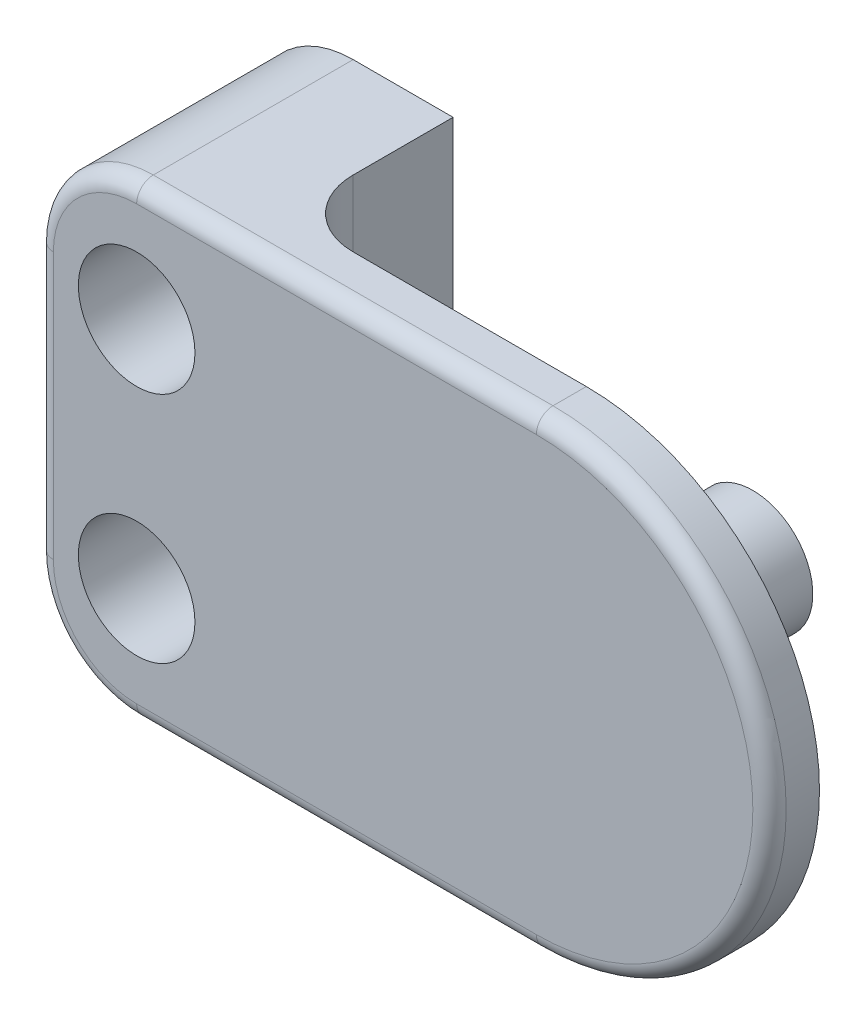
SolidWorks part; units mm, degrees
ref_plane "Front Plane" through (0, 0, 0) normal (0, 0, 1) x (1, 0, 0)
ref_plane "Top Plane" through (0, 0, 0) normal (0, 1, 0) x (1, 0, 0)
ref_plane "Right Plane" through (0, 0, 0) normal (1, 0, 0) x (0, 0, -1)
sketch "Sketch1" plane through (0, 0, 0) normal (0, 0, 1) x (1, 0, 0)
  line L0 (-1.7511, 0) -> (-50001.7511, 0) construction
  line L2 (-15, 7) -> (0, 7)
  line L3 (-15, 7) -> (-15, -7)
  line L4 (-15, -7) -> (0, -7)
  arc A1 (0, 7) -> (0, -7) centre (0, 0) cw
  circle A2 centre (-12, 3.5) radius 1.1
  circle A3 centre (-12, -3.5) radius 1.1
  dimension "D1" = 2.2
  dimension "D2" = 12
  dimension "D3" = 3
  dimension "D4" = 7
  dimension "D5" = 7
extrude "Boss-Extrude1" add sketch "Sketch1" along normal blind 1.5
sketch "Sketch2" plane through (0, 0, 0) normal (0, 0, -1) x (-1, 0, 0)
  circle A0 centre (0, 0) radius 2.5
  dimension "D1" = 5
extrude "Boss-Extrude2" add sketch "Sketch2" along normal blind 1
sketch "Sketch3" plane through (0, 0, -1) normal (0, 0, -1) x (-1, 0, 0)
  line L0 (1.1386, 1.3941) -> (1.1386, -1.3941)
  arc A1 (1.1386, 1.3941) -> (1.1386, -1.3941) centre (0, 0) ccw
  dimension "D1" = 1.8
  dimension "D2" = 1.1386
extrude "Boss-Extrude3" add sketch "Sketch3" along normal blind 4
sketch "Sketch4" plane through (0, 0, 0) normal (0, 0, -1) x (-1, 0, 0)
  line L0 (15, -7) -> (0, -7) construction
  line L1 (15, 7) -> (9, 7)
  line L2 (15, 7) -> (15, -7)
  line L3 (15, -7) -> (9, -7)
  line L4 (9, 7) -> (9, -7)
  circle A0 centre (12, 3.5) radius 1.1
  circle A1 centre (12, -3.5) radius 1.1
  dimension "D1" = 6
extrude "Boss-Extrude4" add sketch "Sketch4" along normal blind 5
fillet "Fillet4" radius 3 2 edges at (-15, 7, -1.75) (-15, -7, -1.75)
fillet "Fillet1" radius 0.5 6 edges at (-6, -7, 1.5) (7, 0, 1.5) (-6, 7, 1.5) (-14.1213, -6.1213, 1.5) (-15, 0, 1.5) (-14.1213, 6.1213, 1.5)
sketch "Sketch5" plane through (0, 0, 1.5) normal (0, 0, 1) x (1, 0, 0)
  circle A0 centre (-12, 3.5) radius 1.75
  circle A1 centre (-12, -3.5) radius 1.75
  dimension "D1" = 3.5
extrude "Cut-Extrude1" cut sketch "Sketch5" against normal blind 4
fillet "Fillet3" radius 2 1 edges at (-9, 0, 0)
